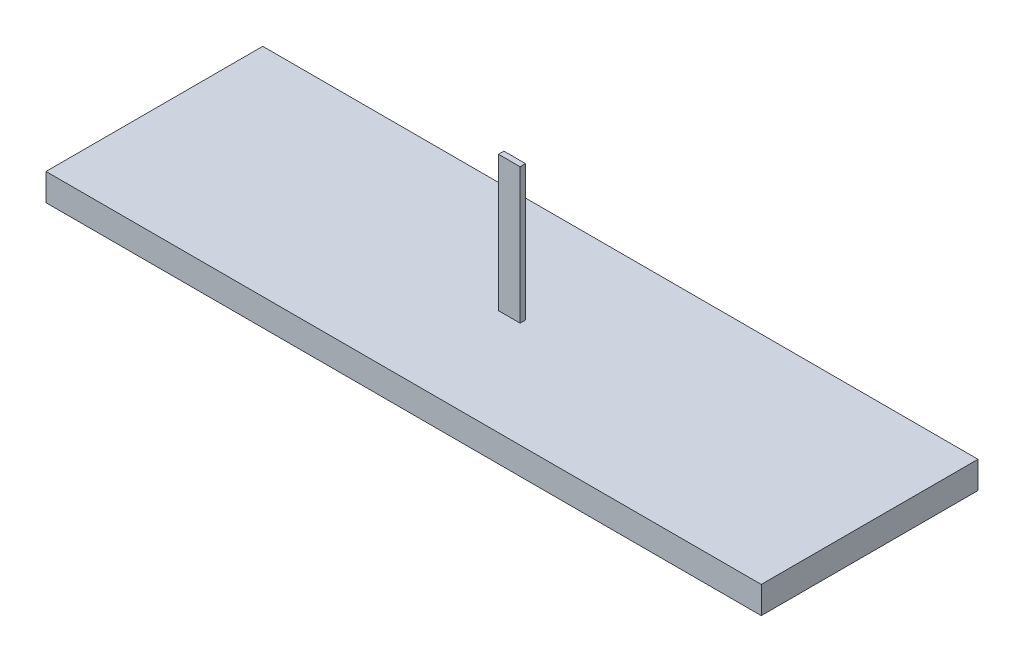
SolidWorks part; units mm, degrees
ref_plane "Front" through (0, 0, 0) normal (0, 0, 1) x (1, 0, 0)
ref_plane "Top" through (0, 0, 0) normal (0, 1, 0) x (1, 0, 0)
ref_plane "Right" through (0, 0, 0) normal (1, 0, 0) x (0, 0, -1)
sketch "Sketch1" plane through (0, 0, 0) normal (0, 1, 0) x (1, 0, 0)
  line L1 (-66, 20) -> (66, 20)
  line L2 (-66, 20) -> (-66, -20)
  line L3 (-66, -20) -> (66, -20)
  line L4 (66, 20) -> (66, -20)
  line L5 (-66, 20) -> (66, -20) construction
  line L6 (-66, -20) -> (66, 20) construction
  point P0 (0, 0)
  dimension "D1" = 40
  dimension "D2" = 132
extrude "Boss-Extrude1" add sketch "Sketch1" along normal blind 5
sketch "Sketch2" plane through (0, 0, 0) normal (0, 0, 1) x (1, 0, 0)
  line L0 (0, -50) -> (0, 50) construction
  line L1 (-2, 30) -> (2, 30)
  line L2 (-2, 30) -> (-2, 0)
  line L3 (-2, 0) -> (2, 0)
  line L4 (2, 30) -> (2, 0)
  line L5 (-2, 30) -> (2, 0) construction
  line L6 (-2, 0) -> (2, 30) construction
  line L7 (50, 0) -> (-50, 0) construction
  point P0 (0, 15)
  dimension "D1" = 30
  dimension "D2" = 4
extrude "Boss-Extrude2" add sketch "Sketch2" along normal blind 0.5 and the other way blind 0.5
